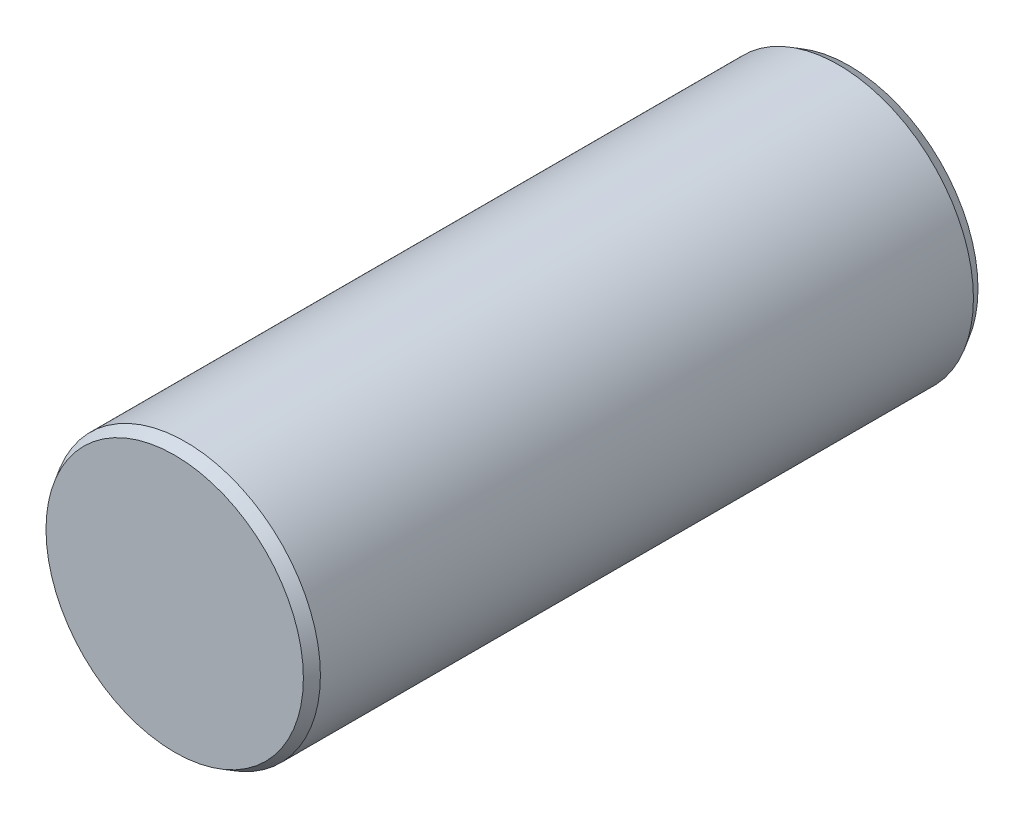
SolidWorks part; units mm, degrees
material "1023 Tôle d'acier au carbone (SS)"
ref_plane "Plan de face" through (0, 0, 0) normal (0, 0, 1) x (1, 0, 0)
ref_plane "Plan de dessus" through (0, 0, 0) normal (0, 1, 0) x (1, 0, 0)
ref_plane "Plan de droite" through (0, 0, 0) normal (1, 0, 0) x (0, 0, -1)
sketch "Esquisse1" plane through (0, 0, 0) normal (0, 0, 1) x (1, 0, 0)
  circle A0 centre (0, 0) radius 2.5
  dimension "D1" = 5
extrude "Boss.-Extru.1" add sketch "Esquisse1" along normal mid plane 12.5
chamfer "Chanfrein1" distance 0.2 angle 30 2 edges at (2.5, 0, -6.25) (2.5, 0, 6.25)
